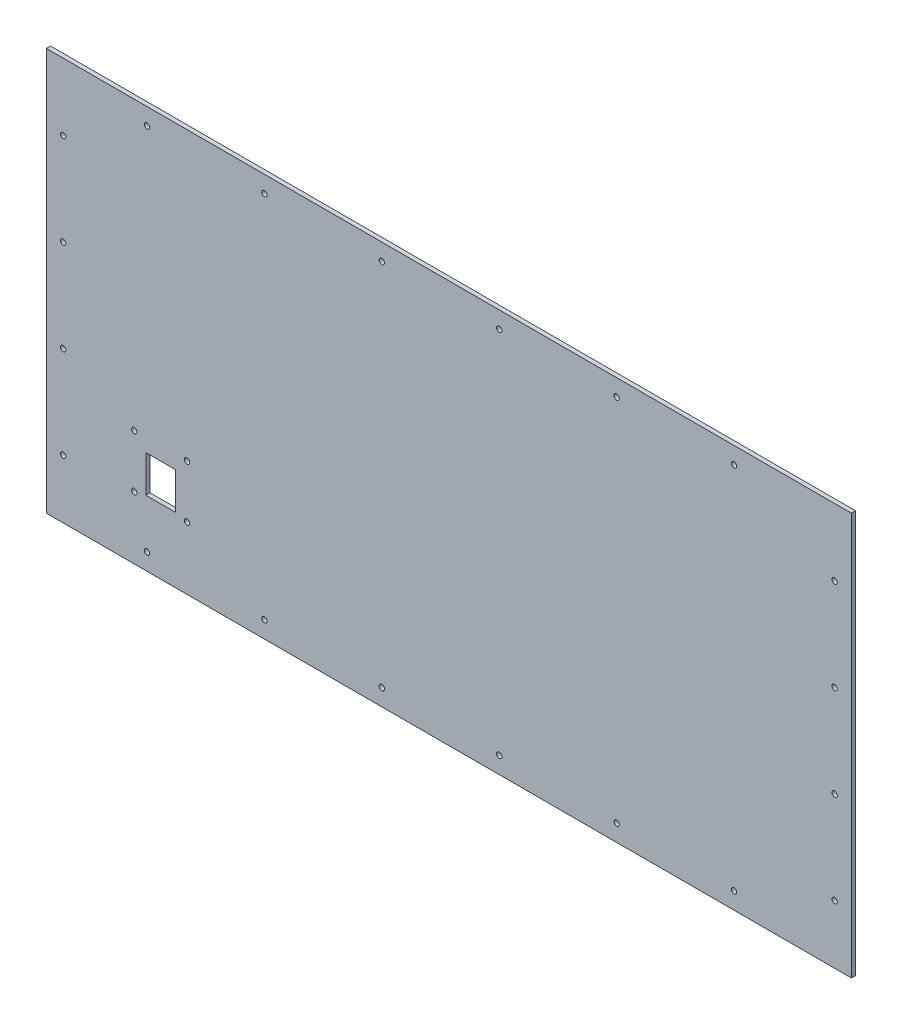
SolidWorks part; units mm, degrees
ref_plane "Front Plane" through (0, 0, 0) normal (0, 0, 1) x (1, 0, 0)
ref_plane "Top Plane" through (0, 0, 0) normal (0, 1, 0) x (1, 0, 0)
ref_plane "Right Plane" through (0, 0, 0) normal (1, 0, 0) x (0, 0, -1)
sketch "Sketch1" plane through (0, 0, 0) normal (0, 0, 1) x (1, 0, 0)
  line L1 (0, 0) -> (-609.6, 0)
  line L2 (0, 0) -> (0, 304.8)
  line L3 (0, 304.8) -> (-609.6, 304.8)
  line L4 (-609.6, 0) -> (-609.6, 304.8)
  dimension "D1" = 609.6
  dimension "D2" = 304.8
extrude "Boss-Extrude1" add sketch "Sketch1" along normal blind 3.175
sketch "Sketch5" plane through (0, 0, 3.175) normal (0, 0, 1) x (1, 0, 0)
  line L0 (-609.6, 304.8) -> (-609.6, 0) construction
  line L1 (-609.6, 0) -> (0, 0) construction
  line L2 (-609.6, 152.4) -> (0, 152.4) construction
  line L3 (0, 0) -> (0, 304.8) construction
  circle A0 centre (-533.4, 12.7) radius 2.032
  circle A1 centre (-444.5, 12.7) radius 2.032
  circle A2 centre (-355.6, 12.7) radius 2.032
  circle A3 centre (-266.7, 12.7) radius 2.032
  circle A4 centre (-177.8, 12.7) radius 2.032
  circle A5 centre (-88.9, 12.7) radius 2.032
  circle A6 centre (-88.9, 292.1) radius 2.032
  circle A7 centre (-177.8, 292.1) radius 2.032
  circle A8 centre (-266.7, 292.1) radius 2.032
  circle A9 centre (-355.6, 292.1) radius 2.032
  circle A10 centre (-444.5, 292.1) radius 2.032
  circle A11 centre (-533.4, 292.1) radius 2.032
  dimension "D1" = 4.064
  dimension "D2" = 76.2
  dimension "D5" = 88.9
  dimension "D4" = 12.7
  dimension "D3" = 6
extrude "Cut-Extrude4" cut sketch "Sketch5" against normal through all
sketch "Sketch6" plane through (0, 0, 3.175) normal (0, 0, 1) x (1, 0, 0)
  line L0 (-609.6, 304.8) -> (-609.6, 0) construction
  line L1 (0, 304.8) -> (-609.6, 304.8) construction
  line L2 (-304.8, 304.8) -> (-304.8, 0) construction
  line L3 (-609.6, 0) -> (0, 0) construction
  circle A0 centre (-596.9, 254) radius 2.032
  circle A1 centre (-596.9, 184.15) radius 2.032
  circle A2 centre (-596.9, 114.3) radius 2.032
  circle A3 centre (-596.9, 44.45) radius 2.032
  circle A4 centre (-12.7, 44.45) radius 2.032
  circle A5 centre (-12.7, 114.3) radius 2.032
  circle A6 centre (-12.7, 184.15) radius 2.032
  circle A7 centre (-12.7, 254) radius 2.032
  dimension "D1" = 4.064
  dimension "D3" = 50.8
  dimension "D5" = 69.85
  dimension "D2" = 12.7
  dimension "D4" = 4
extrude "Cut-Extrude5" cut sketch "Sketch6" against normal blind 3.175
sketch "Sketch7" plane through (0, 0, 3.175) normal (0, 0, 1) x (1, 0, 0)
  line L0 (-523.1, 90.45) -> (-523.1, 44.45) construction
  line L1 (-546.1, 90.45) -> (-500.1, 90.45)
  line L2 (-546.1, 90.45) -> (-546.1, 44.45)
  line L3 (-546.1, 44.45) -> (-500.1, 44.45)
  line L4 (-500.1, 90.45) -> (-500.1, 44.45)
  line L5 (-546.1, 67.45) -> (-500.1, 67.45) construction
  line L7 (-511.8617, 49.45) -> (-534.3383, 49.45)
  line L8 (-511.8617, 49.45) -> (-511.8617, 77.3993)
  line L9 (-511.8617, 77.3993) -> (-534.3383, 77.3993)
  line L10 (-534.3383, 49.45) -> (-534.3383, 77.3993)
  line L11 (-511.8617, 49.45) -> (-534.3383, 77.3993) construction
  line L12 (-511.8617, 77.3993) -> (-534.3383, 49.45) construction
  circle A0 centre (-533.4, 12.7) radius 2.032 construction
  circle A1 centre (-596.9, 44.45) radius 2.032 construction
  circle A2 centre (-543.1, 87.45) radius 2.032
  circle A3 centre (-503.1, 87.45) radius 2.032
  circle A4 centre (-503.1, 47.45) radius 2.032
  circle A5 centre (-543.1, 47.45) radius 2.032
  point P20 (-523.1, 63.4247)
  dimension "D3" = 31.75
  dimension "D5" = 4.064
  dimension "D1" = 46
  dimension "D2" = 46
  dimension "D4" = 50.8
  dimension "D6" = 3
  dimension "D7" = 3
  dimension "D8" = 5
  dimension "D9" = 22.4767
  dimension "D10" = 27.9493
extrude "Cut-Extrude7" cut sketch "Sketch7" against normal through all contours L8 L7 L10 L9 | A2 | A3 | A4 | A5
